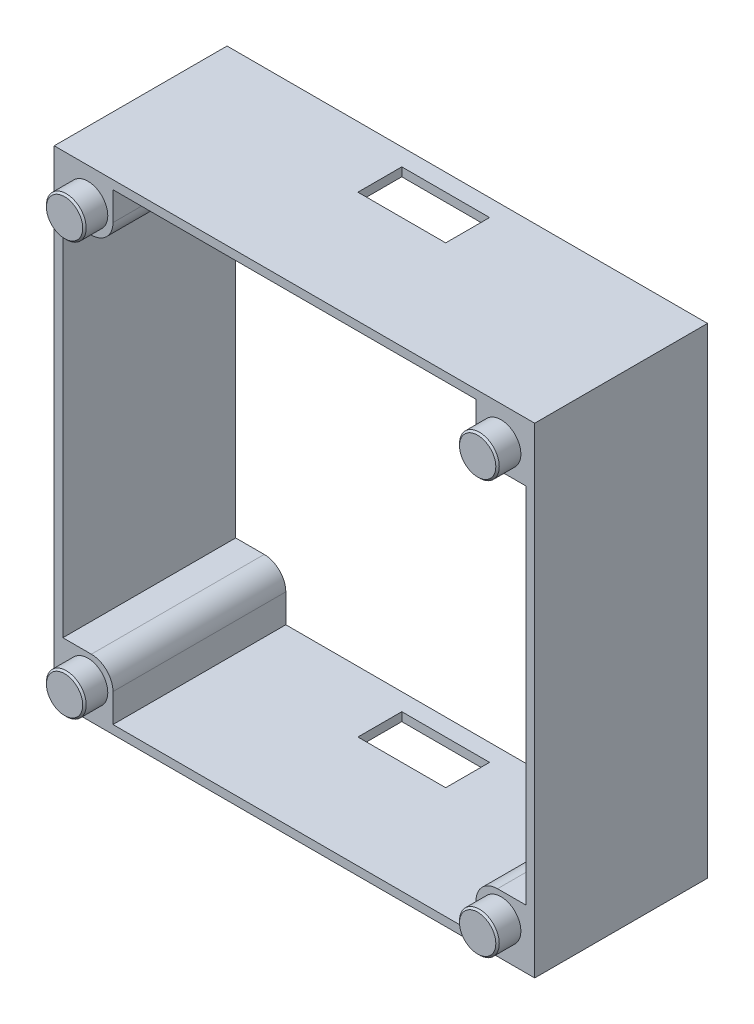
SolidWorks part; units mm, degrees
ref_plane "Přední rovina" through (0, 0, 0) normal (0, 0, 1) x (1, 0, 0)
ref_plane "Horní rovina" through (0, 0, 0) normal (0, 1, 0) x (1, 0, 0)
ref_plane "Pravá rovina" through (0, 0, 0) normal (1, 0, 0) x (0, 0, -1)
sketch "Skica1" plane through (0, 0, 0) normal (0, 0, 1) x (1, 0, 0)
  line L0 (21, -27.8) -> (21, -21)
  line L1 (-27.8, 27.8) -> (27.8, 27.8)
  line L2 (-27.8, 27.8) -> (-27.8, -27.8)
  line L3 (-27.8, -27.8) -> (27.8, -27.8)
  line L4 (27.8, 27.8) -> (27.8, -27.8)
  line L5 (-27.8, 27.8) -> (27.8, -27.8) construction
  line L6 (-27.8, -27.8) -> (27.8, 27.8) construction
  line L7 (-26.8, 26.8) -> (26.8, 26.8)
  line L8 (-26.8, 26.8) -> (-26.8, -26.8)
  line L9 (-26.8, -26.8) -> (26.8, -26.8)
  line L10 (26.8, 26.8) -> (26.8, -26.8)
  line L11 (-26.8, 26.8) -> (26.8, -26.8) construction
  line L12 (-26.8, -26.8) -> (26.8, 26.8) construction
  line L13 (-27.8, 27.8) -> (-21, 27.8)
  line L14 (-27.8, 27.8) -> (-27.8, 21)
  line L15 (-27.8, 21) -> (-21, 21)
  line L16 (-21, 27.8) -> (-21, 21)
  line L17 (27.8, -21) -> (21, -21)
  line L18 (27.8, -27.8) -> (27.8, -21)
  line L19 (27.8, -27.8) -> (21, -27.8)
  line L20 (27.8, 27.8) -> (21, 27.8)
  line L21 (27.8, 27.8) -> (27.8, 21)
  line L22 (27.8, 21) -> (21, 21)
  line L23 (21, 27.8) -> (21, 21)
  line L24 (27.8, -27.8) -> (27.8, -21)
  line L25 (27.8, -27.8) -> (21, -27.8)
  line L26 (21, -27.8) -> (21, -21)
  line L27 (27.8, -21) -> (21, -21)
  line L28 (-27.8, -27.8) -> (-21, -27.8)
  line L29 (-27.8, -27.8) -> (-27.8, -21)
  line L30 (-27.8, -21) -> (-21, -21)
  line L31 (-21, -27.8) -> (-21, -21)
  point P0 (0, 0)
  point P5 (0, 0)
  point P32 (0, 0)
  dimension "D1" = 55.6
  dimension "D2" = 53.6
  dimension "D3" = 6.8
  dimension "D4" = 4
extrude "Přidat vysunutím2" add sketch "Skica1" along normal blind 20 contours L16 L1 L2 L15 L8 L7 | L16 L7 L8 L15 | L1 L23 L7 L10 L22 L4 | L7 L23 L22 L10 | L4 L17 L10 L9 L0 L3 | L10 L17 L0 L9 | L9 L31 L30 L8 | L3 L31 L9 L8 L30 L2 | L2 L30 L8 L15 | L31 L3 L0 L9 | L4 L22 L10 L17 | L23 L1 L16 L7
fillet "Zaoblit1" radius 2.5 4 edges at (-21, -21, 10) (21, -21, 10) (21, 21, 10) (-21, 21, 10)
sketch "Skica2" plane through (0, 0, 0) normal (0, 0, -1) x (-1, 0, 0)
  line L0 (-27.8, 27.8) -> (-27.8, -27.8) construction
  line L1 (27.8, 27.8) -> (-27.8, 27.8) construction
  circle A0 centre (-23.9, 23.9) radius 2.4
  circle A4 centre (23.9, 23.9) radius 2.4
  circle A5 centre (23.9, -23.9) radius 2.4
  circle A6 centre (-23.9, -23.9) radius 2.4
  point P15 (-0.2487, -0.2461)
  point P16 (0, 0)
  dimension "D1" = 4.8
  dimension "D2" = 3.9
  dimension "D3" = 3.9
  dimension "D4" = 4
extrude "Odebrat vysunutím1" cut sketch "Skica2" against normal blind 1.9
sketch "Skica3" plane through (0, 0, 20) normal (0, 0, 1) x (1, 0, 0)
  line L0 (-27.8, 27.8) -> (-27.8, -27.8) construction
  line L1 (-27.8, 27.8) -> (27.8, 27.8) construction
  circle A0 centre (-23.9, 23.9) radius 2.3
  circle A4 centre (23.9, 23.9) radius 2.3
  circle A5 centre (23.9, -23.9) radius 2.3
  circle A6 centre (-23.9, -23.9) radius 2.3
  point P15 (-0.5, 0)
  point P16 (0, 0)
  dimension "D1" = 4.6
  dimension "D2" = 3.9
  dimension "D3" = 3.9
  dimension "D4" = 4
extrude "Přidat vysunutím3" add sketch "Skica3" along normal blind 2.7
chamfer "Zkosení1" distance 0.2 angle 45 4 edges at (-21.6, 23.9, 22.7) (-21.6, -23.9, 22.7) (26.2, -23.9, 22.7) (26.2, 23.9, 22.7)
sketch "Skica4" plane through (0, -27.8, 0) normal (0, -1, 0) x (-1, 0, 0)
  line L0 (27.8, -20) -> (27.8, 0) construction
  line L1 (5.58, -7.08) -> (-4.58, -7.08)
  line L2 (5.58, -7.08) -> (5.58, -2)
  line L3 (5.58, -2) -> (-4.58, -2)
  line L4 (-4.58, -7.08) -> (-4.58, -2)
  line L5 (-27.8, -20) -> (-27.8, 0) construction
  line L6 (27.8, 0) -> (-27.8, 0) construction
  dimension "D1" = 5.08
  dimension "D2" = 10.16
  dimension "D3" = 22.22
  dimension "D4" = 23.22
  dimension "D5" = 2
extrude "Odebrat vysunutím2" cut sketch "Skica4" against normal blind 68.7
